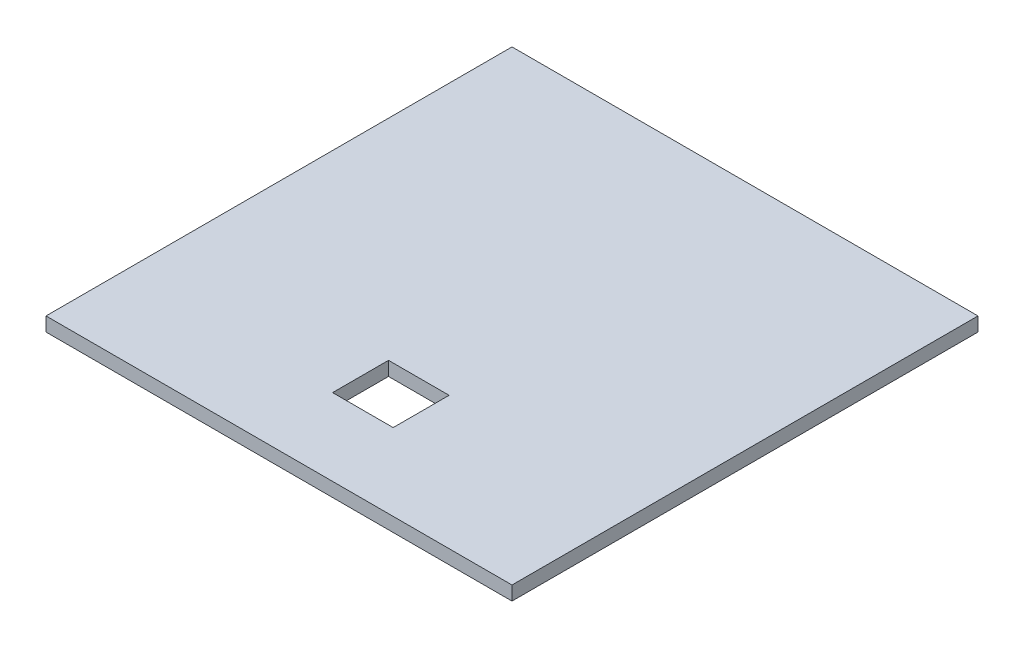
SolidWorks part; units mm, degrees
ref_plane "Front Plane" through (0, 0, 0) normal (0, 0, 1) x (1, 0, 0)
ref_plane "Top Plane" through (0, 0, 0) normal (0, 1, 0) x (1, 0, 0)
ref_plane "Right Plane" through (0, 0, 0) normal (1, 0, 0) x (0, 0, -1)
sketch "Sketch1" plane through (0, 0, 0) normal (0, 1, 0) x (1, 0, 0)
  line L1 (50, 50) -> (-50, 50)
  line L2 (50, 50) -> (50, -50)
  line L3 (50, -50) -> (-50, -50)
  line L4 (-50, 50) -> (-50, -50)
  line L5 (50, 50) -> (-50, -50) construction
  line L6 (50, -50) -> (-50, 50) construction
  point P0 (0, 0)
  dimension "D1" = 100
  dimension "D2" = 100
extrude "Boss-Extrude1" add sketch "Sketch1" along normal blind 3
sketch "Sketch2" plane through (0, 3, 0) normal (0, 1, 0) x (1, 0, 0)
  line L0 (50, -50) -> (50, 50) construction
  line L1 (-50, -50) -> (50, -50) construction
  line L2 (25, -40) -> (25, 8.3) construction
  circle A0 centre (-27.4, -7) radius 1.6
  circle A1 centre (-27.4, -34.9) radius 1.6
  circle A2 centre (23.4, 8.3) radius 1.6
  circle A3 centre (25, -40) radius 1.6
  dimension "D1" = 3.2
  dimension "D2" = 50.8
  dimension "D3" = 27.9
  dimension "D7" = 5.1
  dimension "D4" = 48.3
  dimension "D5" = 25
  dimension "D6" = 10
extrude "Cut-Extrude1" [suppressed] cut sketch "Sketch2" against normal through all
sketch "Sketch3" plane through (0, 0, 0) normal (0, -1, 0) x (1, 0, 0)
  line L0 (-50, 50) -> (50, 50) construction
  line L1 (-5, 33.5) -> (8, 33.5)
  line L2 (-5, 33.5) -> (-5, 21.5)
  line L3 (-5, 21.5) -> (8, 21.5)
  line L4 (8, 33.5) -> (8, 21.5)
  line L5 (-5, 33.5) -> (8, 21.5) construction
  line L6 (-5, 21.5) -> (8, 33.5) construction
  line L7 (50, 50) -> (50, -50) construction
  point P0 (1.5, 27.5)
  dimension "D1" = 12
  dimension "D2" = 13
  dimension "D3" = 16.5
  dimension "D4" = 42
extrude "Cut-Extrude3" cut sketch "Sketch3" against normal up to surface (3 mm away) contours L3 L4 L1 L2 up to face at (0, 3, 0)
